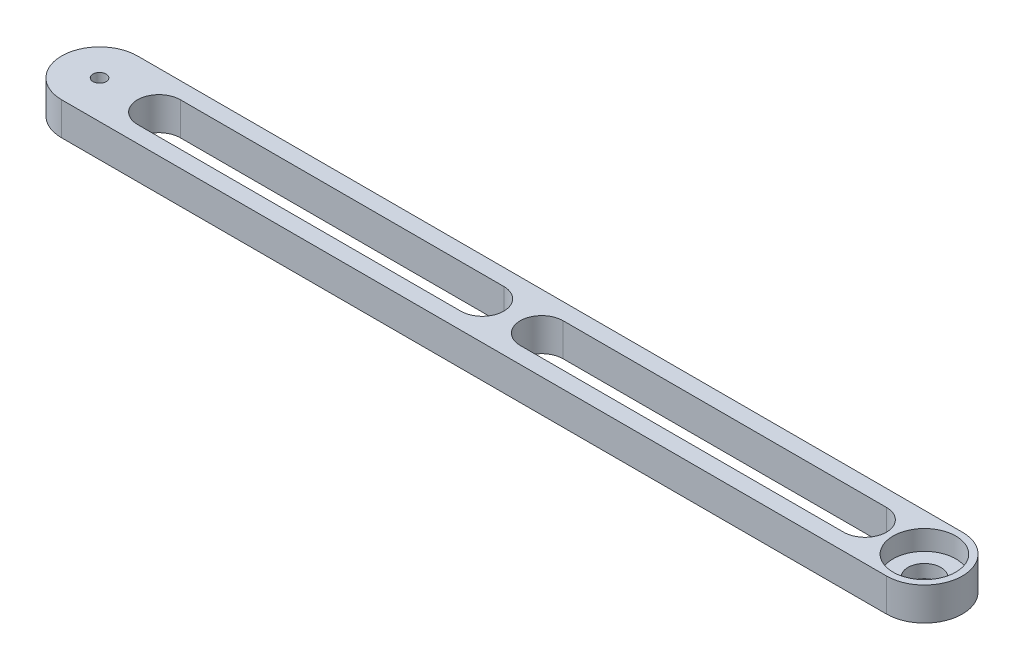
SolidWorks part; units mm, degrees
material "6061 Alloy"
ref_plane "Front Plane" through (0, 0, 0) normal (0, 0, 1) x (1, 0, 0)
ref_plane "Top Plane" through (0, 0, 0) normal (0, 1, 0) x (1, 0, 0)
ref_plane "Right Plane" through (0, 0, 0) normal (1, 0, 0) x (0, 0, -1)
sketch "Sketch1" plane through (0, 0, 0) normal (0, 1, 0) x (1, 0, 0)
  line L0 (0, 11.5) -> (250, 11.5)
  line L1 (0, -11.5) -> (250, -11.5)
  arc A0 (0, 11.5) -> (0, -11.5) centre (0, 0) ccw
  arc A1 (250, -11.5) -> (250, 11.5) centre (250, 0) ccw
  circle A2 centre (0, 0) radius 2
  dimension "D1" = 23
  dimension "D2" = 23
  dimension "D4" = 4
  dimension "D3" = 250
extrude "Boss-Extrude1" add sketch "Sketch1" along normal blind 10
sketch "Sketch2" plane through (0, 10, 0) normal (0, 1, 0) x (1, 0, 0)
  circle A0 centre (250, 0) radius 9.5
  dimension "D1" = 19
extrude "Cut-Extrude1" cut sketch "Sketch2" against normal blind 6
sketch "Sketch3" plane through (0, 0, 0) normal (0, -1, 0) x (-1, 0, 0)
  circle A0 centre (-250, 0) radius 5
  dimension "D1" = 10
extrude "Cut-Extrude2" cut sketch "Sketch3" against normal through all
sketch "Sketch4" plane through (0, 10, 0) normal (0, 1, 0) x (1, 0, 0)
  line L0 (0, 0) -> (250, 0) construction
  line L1 (18, 0) -> (116, 0) construction
  line L2 (18, 6.5) -> (116, 6.5)
  line L3 (18, -6.5) -> (116, -6.5)
  line L4 (134, 0) -> (232, 0) construction
  line L5 (134, 6.5) -> (232, 6.5)
  line L6 (134, -6.5) -> (232, -6.5)
  line L7 (250, 11.5) -> (0, 11.5) construction
  arc A0 (18, 6.5) -> (18, -6.5) centre (18, 0) ccw
  arc A1 (116, -6.5) -> (116, 6.5) centre (116, 0) ccw
  arc A2 (134, 6.5) -> (134, -6.5) centre (134, 0) ccw
  arc A3 (232, -6.5) -> (232, 6.5) centre (232, 0) ccw
  point P6 (67, 0)
  point P13 (183, 0)
  point P20 (11.5, 0)
  point P21 (238.5, 0)
  point P22 (122.5, 0)
  point P23 (127.5, 0)
  dimension "D4" = 5
  dimension "D1" = 5
  dimension "D2" = 11.5
  dimension "D3" = 11.5
extrude "Cut-Extrude3" cut sketch "Sketch4" against normal through all
